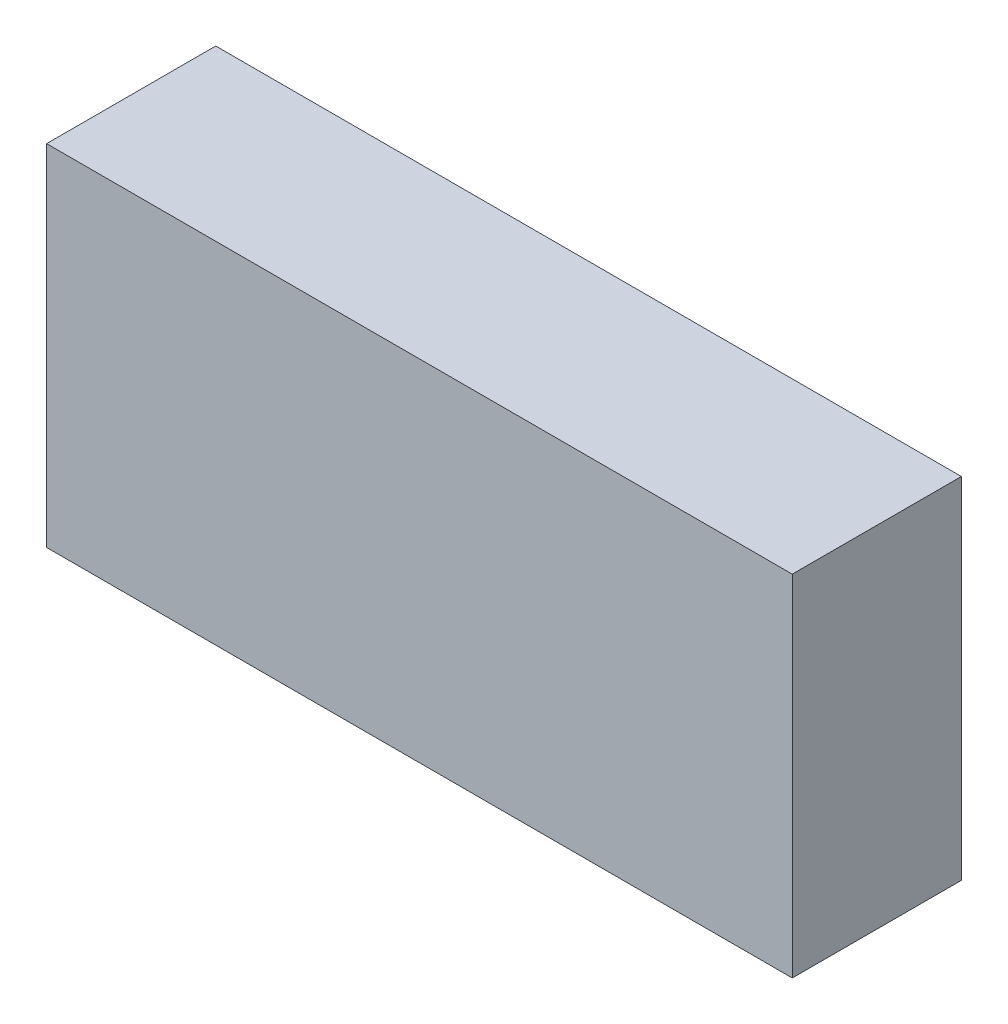
SolidWorks part; units mm, degrees
ref_plane "Front Plane" through (0, 0, 0) normal (0, 0, 1) x (1, 0, 0)
ref_plane "Top Plane" through (0, 0, 0) normal (0, 1, 0) x (1, 0, 0)
ref_plane "Right Plane" through (0, 0, 0) normal (1, 0, 0) x (0, 0, -1)
sketch "Sketch1" plane through (0, 0, 0) normal (0, 0, 1) x (1, 0, 0)
  line L1 (-97, -45.5) -> (97, -45.5)
  line L2 (-97, -45.5) -> (-97, 45.5)
  line L3 (-97, 45.5) -> (97, 45.5)
  line L4 (97, -45.5) -> (97, 45.5)
  line L5 (-97, -45.5) -> (97, 45.5) construction
  line L6 (-97, 45.5) -> (97, -45.5) construction
  point P0 (0, 0)
  dimension "D1" = 194
  dimension "D2" = 91
extrude "Boss-Extrude1" add sketch "Sketch1" along normal blind 44
sketch "Sketch4" plane through (0, 0, 44) normal (0, 0, 1) x (1, 0, 0)
  text T0 "MAXAMPS 23 aH Battery\r\n"
